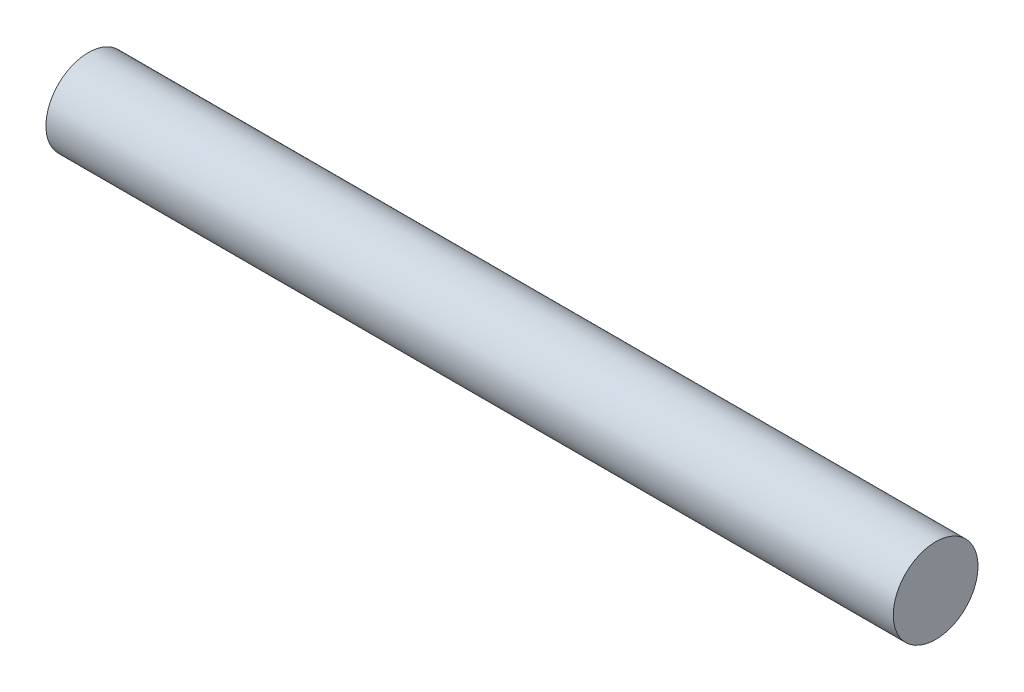
SolidWorks part; units mm, degrees
material "6061 Alloy"
ref_plane "Front Plane" through (0, 0, 0) normal (0, 0, 1) x (1, 0, 0)
ref_plane "Top Plane" through (0, 0, 0) normal (0, 1, 0) x (1, 0, 0)
ref_plane "Right Plane" through (0, 0, 0) normal (1, 0, 0) x (0, 0, -1)
sketch "Sketch1" plane through (0, 0, 0) normal (1, 0, 0) x (0, 0, -1)
  circle A0 centre (0, 0) radius 0.75
  dimension "D1" = 1.5
extrude "Boss-Extrude1" add sketch "Sketch1" along normal blind 15
ref_plane "Plane Mate for Bar" through (7.5, 0, 0) normal (1, 0, 0) x (0, 0, -1)
